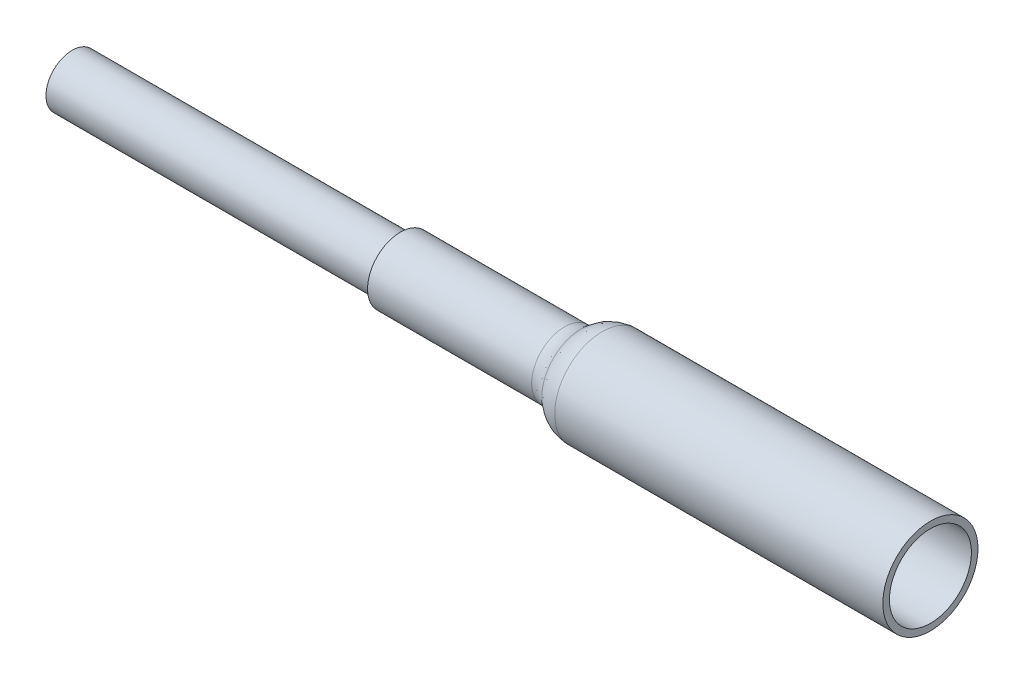
SolidWorks part; units mm, degrees
ref_plane "Front Plane" through (0, 0, 0) normal (0, 0, 1) x (1, 0, 0)
ref_plane "Top Plane" through (0, 0, 0) normal (0, 1, 0) x (1, 0, 0)
ref_plane "Right Plane" through (0, 0, 0) normal (1, 0, 0) x (0, 0, -1)
sketch "Sketch1" plane through (0, 0, 0) normal (0, 1, 0) x (1, 0, 0)
  line L0 (0, 0) -> (0, 1.016)
  line L1 (0, 1.016) -> (12.7, 1.016)
  line L2 (12.7, 1.016) -> (12.7, 1.27)
  line L3 (12.7, 1.27) -> (19.05, 1.27)
  line L4 (20.5133, 1.8415) -> (33.2133, 1.8415)
  line L5 (33.2133, 1.8415) -> (33.2133, 1.5875)
  line L6 (33.2133, 1.5875) -> (20.5133, 1.5875)
  line L7 (19.05, 1.016) -> (20.5133, 1.016)
  line L8 (20.5133, 1.016) -> (20.5133, 0.635)
  line L9 (20.5133, 0.635) -> (25.5933, 0.635)
  line L10 (25.5933, 0.635) -> (25.5933, 0)
  line L11 (25.5933, 0) -> (0, 0)
  arc A0 (19.05, 1.27) -> (19.6956, 1.5221) centre (19.05, 2.2225) ccw
  arc A1 (19.6956, 1.5221) -> (20.5133, 1.8415) centre (20.5133, 0.635) cw
  arc A2 (20.5133, 1.5875) -> (19.8677, 1.3354) centre (20.5133, 0.635) ccw
  arc A3 (19.8677, 1.3354) -> (19.05, 1.016) centre (19.05, 2.2225) cw
  point P21 (0, 0)
  point P22 (20.3441, 2.2225)
  dimension "D1" = 12.7
  dimension "D2" = 0.635
  dimension "D3" = 1.5875
  dimension "D4" = 0.254
  dimension "D5" = 6.35
  dimension "D6" = 12.7
  dimension "D7" = 5.08
  dimension "D8" = 1.016
revolve "Revolve1" add sketch "Sketch1" angle 360 about L11
